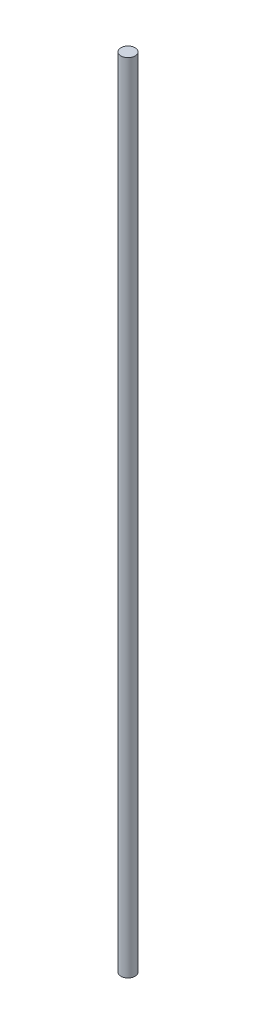
SolidWorks part; units mm, degrees
ref_plane "Front Plane" through (0, 0, 0) normal (0, 0, 1) x (1, 0, 0)
ref_plane "Top Plane" through (0, 0, 0) normal (0, 1, 0) x (1, 0, 0)
ref_plane "Right Plane" through (0, 0, 0) normal (1, 0, 0) x (0, 0, -1)
sketch "Sketch1" plane through (0, 0, 0) normal (0, 1, 0) x (1, 0, 0)
  circle A0 centre (0, 0) radius 2.5
  dimension "D1" = 5
extrude "Boss-Extrude1" add sketch "Sketch1" along normal blind 279.4
cosmetic thread "Cosmetic Thread2"
cosmetic thread "Cosmetic Thread3"
